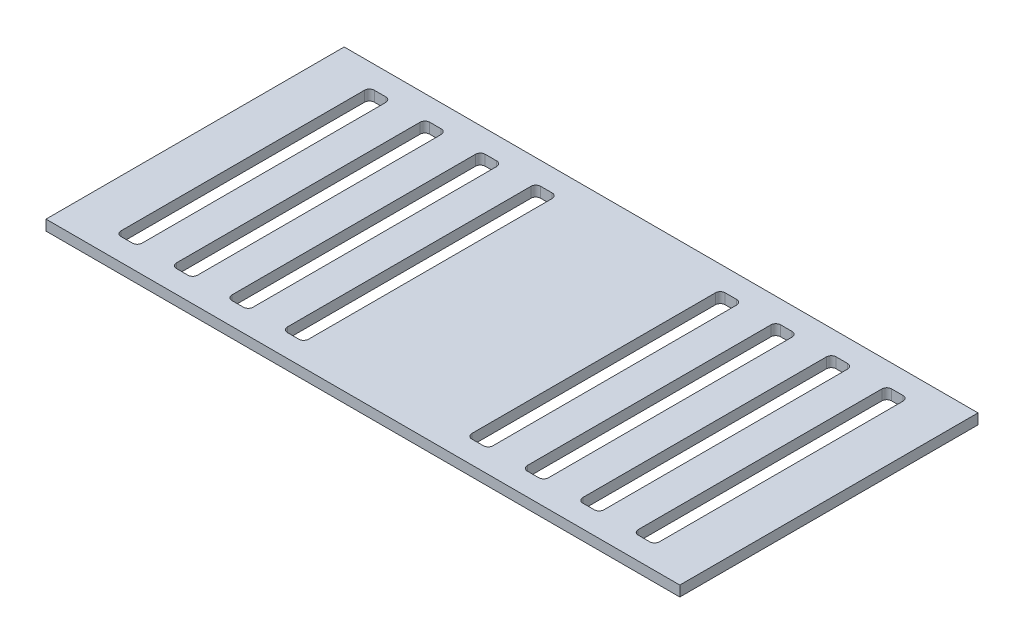
SolidWorks part; units mm, degrees
ref_plane "Front Plane" through (0, 0, 0) normal (0, 0, 1) x (1, 0, 0)
ref_plane "Top Plane" through (0, 0, 0) normal (0, 1, 0) x (1, 0, 0)
ref_plane "Right Plane" through (0, 0, 0) normal (1, 0, 0) x (0, 0, -1)
sketch "Sketch1" plane through (0, 0, 0) normal (0, 1, 0) x (1, 0, 0)
  line L1 (-457, -215) -> (457, -215)
  line L2 (-457, -215) -> (-457, 215)
  line L3 (-457, 215) -> (457, 215)
  line L4 (457, -215) -> (457, 215)
  line L5 (-457, -215) -> (457, 215) construction
  line L6 (-457, 215) -> (457, -215) construction
  point P0 (0, 0)
  dimension "D1" = 914
  dimension "D2" = 430
extrude "Boss-Extrude1" add sketch "Sketch1" along normal blind 15
sketch "Sketch2" plane through (0, 15, 0) normal (0, 1, 0) x (1, 0, 0)
  line L1 (364.7269, -182.6853) -> (381.3018, -182.6853)
  line L2 (357.7269, -175.6853) -> (357.7269, 175.6853)
  line L3 (364.7269, 182.6853) -> (381.3018, 182.6853)
  line L4 (388.3018, -175.6853) -> (388.3018, 175.6853)
  line L5 (357.7269, -182.6853) -> (388.3018, 182.6853) construction
  line L6 (357.7269, 182.6853) -> (388.3018, -182.6853) construction
  arc A0 (364.7269, -182.6853) -> (357.7269, -175.6853) centre (364.7269, -175.6853) cw
  arc A1 (381.3018, -182.6853) -> (388.3018, -175.6853) centre (381.3018, -175.6853) ccw
  arc A2 (381.3018, 182.6853) -> (388.3018, 175.6853) centre (381.3018, 175.6853) cw
  arc A3 (364.7269, 182.6853) -> (357.7269, 175.6853) centre (364.7269, 175.6853) ccw
  point P0 (373.0143, 0)
  dimension "D1" = 7
extrude "Cut-Extrude2" cut sketch "Sketch2" against normal through all
pattern_linear "LPattern1" count 4 spacing 80 along (-1, 0, 0) of "Cut-Extrude2"
ref_plane "Plane1" through (0, 0, 0) normal (1, 0, 0) x (0, 0, -1)
mirror "Mirror1" about plane through (0, 0, 0) normal (1, 0, 0) of "Cut-Extrude2", "LPattern1"
